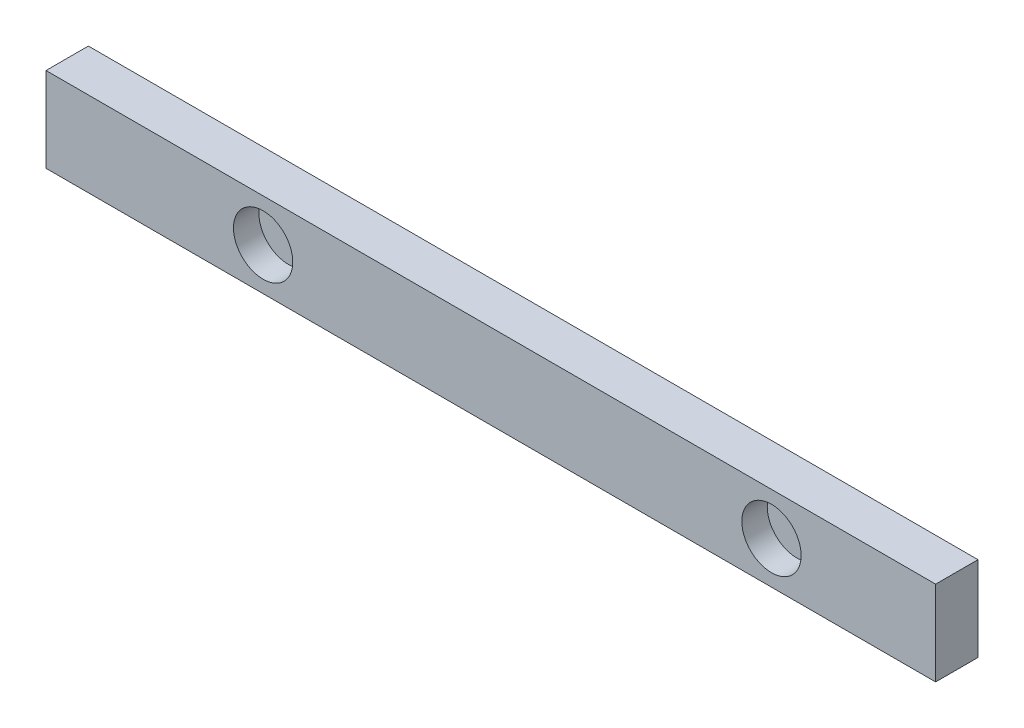
SolidWorks part; units mm, degrees
ref_plane "Front Plane" through (0, 0, 0) normal (0, 0, 1) x (1, 0, 0)
ref_plane "Top Plane" through (0, 0, 0) normal (0, 1, 0) x (1, 0, 0)
ref_plane "Right Plane" through (0, 0, 0) normal (1, 0, 0) x (0, 0, -1)
sketch "Sketch1" plane through (0, 0, 0) normal (0, 0, 1) x (1, 0, 0)
  line L1 (0, 0) -> (533.4, 0)
  line L2 (0, 0) -> (0, 50.8)
  line L3 (0, 50.8) -> (533.4, 50.8)
  line L4 (533.4, 0) -> (533.4, 50.8)
  dimension "D1" = 50.8
  dimension "D2" = 533.4
extrude "Boss-Extrude1" add sketch "Sketch1" along normal blind 25.4
sketch "Sketch3" plane through (0, 0, 0) normal (0, 0, -1) x (-1, 0, 0)
  line L1 (-533.4, 0) -> (-533.4, 50.8) construction
  circle A0 centre (-130.175, 25.2907) radius 17.78
  circle A1 centre (-434.975, 25.2907) radius 17.78
  point P6 (0, 0)
  dimension "D1" = 35.56
  dimension "D2" = 403.225
  dimension "D3" = 98.425
extrude "Cut-Extrude1" cut sketch "Sketch3" against normal blind 127 from offset 10.16 offset against normal yes
sketch "Sketch4" plane through (0, 0, 0) normal (0, 0, -1) x (-1, 0, 0)
  line L0 (-533.4, 50.8) -> (0, 50.8) construction
  line L1 (0, 0) -> (-533.4, 0) construction
  line L2 (-130.175, 25.4) -> (-130.175, 0) construction
  line L3 (-130.175, 50.8) -> (-130.175, 25.4) construction
  line L4 (-137.6215, 18.9093) -> (-122.7285, 31.8907) construction
  line L6 (-533.4, 0) -> (-533.4, 50.8) construction
  line L8 (-442.4215, 18.9093) -> (-427.5285, 31.8907) construction
  circle A0 centre (-130.175, 25.4) radius 6.0198
  circle A1 centre (-122.7285, 18.9093) radius 2.4638
  circle A2 centre (-122.7285, 31.8907) radius 2.4638
  circle A3 centre (-137.6215, 18.9093) radius 2.4638
  circle A4 centre (-137.6215, 31.8907) radius 2.4638
  circle A5 centre (-434.975, 25.4) radius 6.0198
  circle A6 centre (-427.5285, 18.9093) radius 2.4638
  circle A7 centre (-427.5285, 31.8907) radius 2.4638
  circle A8 centre (-442.4215, 18.9093) radius 2.4638
  circle A9 centre (-442.4215, 31.8907) radius 2.4638
  point P0 (-130.175, 25.4)
  point P12 (0, 0)
  point P19 (-434.975, 25.4)
  dimension "D1" = 12.0396
  dimension "D2" = 4.9276
  dimension "D3" = 19.7566
  dimension "D4" = 403.225
  dimension "D5" = 19.7566
  dimension "D6" = 98.425
extrude "Cut-Extrude2" cut sketch "Sketch4" against normal blind 7.62
